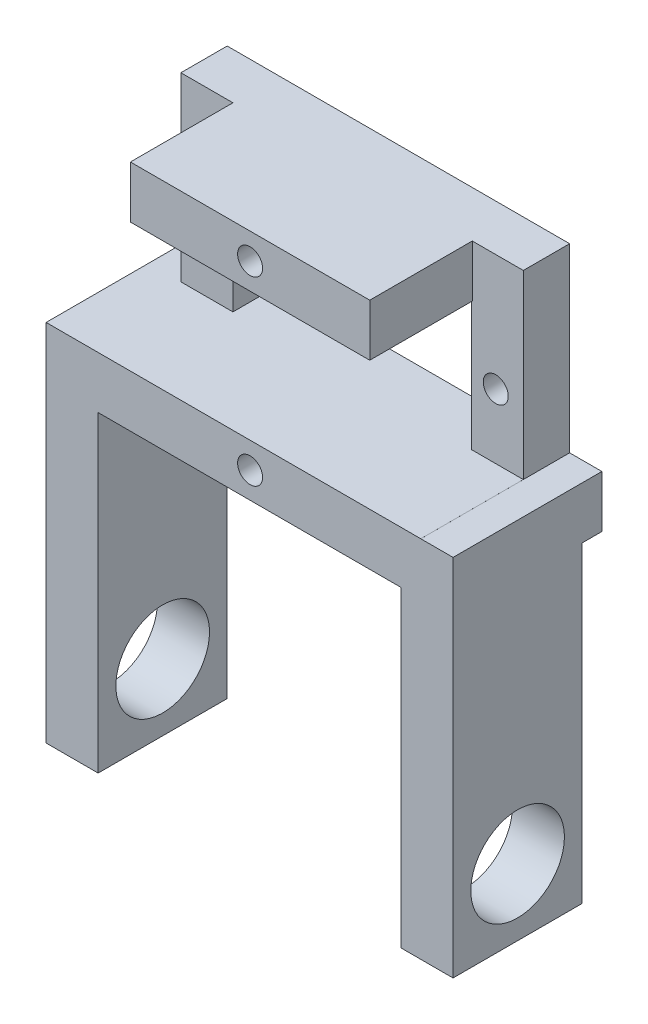
SolidWorks part; units mm, degrees
ref_plane "Front Plane" through (0, 0, 0) normal (0, 0, 1) x (1, 0, 0)
ref_plane "Top Plane" through (0, 0, 0) normal (0, 1, 0) x (1, 0, 0)
ref_plane "Right Plane" through (0, 0, 0) normal (1, 0, 0) x (0, 0, -1)
sketch "Sketch1" plane through (0, 0, 0) normal (0, 0, 1) x (1, 0, 0)
  line L1 (-16.45, 11.2) -> (16.45, 11.2)
  line L2 (-16.45, 11.2) -> (-16.45, -11.2)
  line L3 (-16.45, -11.2) -> (16.45, -11.2)
  line L4 (16.45, 11.2) -> (16.45, -11.2)
  line L5 (-16.45, 11.2) -> (16.45, -11.2) construction
  line L6 (-16.45, -11.2) -> (16.45, 11.2) construction
  point P0 (0, 0)
  dimension "D1" = 32.9
  dimension "22.4" = 22.4
extrude "Boss-Extrude1" add sketch "Sketch1" along normal blind 5
sketch "Sketch2" plane through (0, 0, 5) normal (0, 0, 1) x (1, 0, 0)
  line L0 (0, 0) -> (13.8, 0) construction
  line L1 (-11.45, 6.2) -> (11.45, 6.2)
  line L2 (-11.45, 6.2) -> (-11.45, -6.2)
  line L3 (-11.45, -6.2) -> (11.45, -6.2)
  line L4 (11.45, 6.2) -> (11.45, -6.2)
  line L5 (-11.45, 6.2) -> (11.45, -6.2) construction
  line L6 (-11.45, -6.2) -> (11.45, 6.2) construction
  line L7 (0, 0) -> (-13.8, 0) construction
  circle A0 centre (13.8, 0) radius 1.2
  circle A1 centre (-13.8, 0) radius 1.2
  point P0 (0, 0)
  dimension "D3" = 13.8
  dimension "D1" = 22.9
  dimension "D2" = 13.8
  dimension "12.4" = 12.4
extrude "Cut-Extrude2" cut sketch "Sketch2" against normal blind 5
sketch "Sketch3" plane through (0, 0, 5) normal (0, 0, 1) x (1, 0, 0)
  line L0 (16.45, 11.2) -> (-16.45, 11.2) construction
  line L1 (-11.45, 6.2) -> (11.5469, 6.2)
  line L2 (-11.45, 6.2) -> (-11.45, 11.2)
  line L3 (-11.45, 11.2) -> (11.5469, 11.2)
  line L4 (11.5469, 6.2) -> (11.5469, 11.2)
  line L5 (-16.45, -11.2) -> (16.45, -11.2) construction
  line L6 (-11.45, -6.2) -> (11.5469, -6.2)
  line L7 (-11.45, -6.2) -> (-11.45, -11.2)
  line L8 (-11.45, -11.2) -> (11.5469, -11.2)
  line L9 (11.5469, -6.2) -> (11.5469, -11.2)
extrude "Boss-Extrude2" add sketch "Sketch3" along normal blind 12.3
sketch "Sketch4" plane through (0, 0, 17.3) normal (0, 0, 1) x (1, 0, 0)
  line L0 (0.0484, 11.2) -> (0.0484, 6.2) construction
  line L1 (11.5469, 11.2) -> (-11.45, 11.2) construction
  line L2 (-11.45, 6.2) -> (11.5469, 6.2) construction
  line L3 (0.0484, -6.2) -> (0.0484, -11.2) construction
  line L4 (11.5469, -6.2) -> (-11.45, -6.2) construction
  line L5 (-11.45, -11.2) -> (11.5469, -11.2) construction
  circle A0 centre (0.0484, 8.7) radius 1.2
  circle A1 centre (0.0484, -8.7) radius 1.2
extrude "Cut-Extrude3" cut sketch "Sketch4" against normal blind 5
sketch "Sketch6" plane through (0, 0, 5) normal (0, 0, 1) x (1, 0, 0)
  line L0 (-11.45, 6.2) -> (-11.45, -6.2) construction
  line L1 (-16.45, -11.2) -> (-11.45, -11.2)
  line L2 (-16.45, -11.2) -> (-16.45, -6.2)
  line L3 (-16.45, -6.2) -> (-11.45, -6.2)
  line L4 (-11.45, -11.2) -> (-11.45, -6.2)
  line L5 (-11.45, -6.2) -> (-11.45, -11.2) construction
  line L6 (16.45, -11.2) -> (16.45, 11.2) construction
  line L7 (11.5469, -11.2) -> (16.45, -11.2)
  line L8 (11.5469, -11.2) -> (11.5469, -6.2)
  line L9 (11.5469, -6.2) -> (16.45, -6.2)
  line L10 (16.45, -11.2) -> (16.45, -6.2)
extrude "Boss-Extrude3" add sketch "Sketch6" along normal blind 12.3
sketch "Sketch8" plane through (16.45, 0, 0) normal (1, 0, 0) x (0, 0, -1)
  line L0 (0, -11.2) -> (0, 11.2) construction
  line L1 (-17.3, -11.2) -> (0, -11.2)
  line L2 (-17.3, -11.2) -> (-17.3, -6.2018)
  line L3 (-17.3, -6.2018) -> (0, -6.2018)
  line L4 (0, -11.2) -> (0, -6.2018)
extrude "Boss-Extrude4" add sketch "Sketch8" along normal blind 3.1
sketch "Sketch9" plane through (-16.45, 0, 0) normal (-1, 0, 0) x (0, 0, 1)
  line L1 (0, -11.2) -> (17.3, -11.2)
  line L2 (0, -11.2) -> (0, -6.2)
  line L3 (0, -6.2) -> (17.3, -6.2)
  line L4 (17.3, -11.2) -> (17.3, -6.2)
extrude "Boss-Extrude5" add sketch "Sketch9" along normal blind 3.1
sketch "Sketch10" plane through (0, -11.2, 0) normal (0, -1, 0) x (1, 0, 0)
  line L0 (19.55, 8.65) -> (17.05, 8.65) construction
  line L1 (19.55, 17.3) -> (19.55, 0) construction
  line L2 (-19.55, 8.65) -> (-17.05, 8.65) construction
  line L3 (-19.55, 0) -> (-19.55, 17.3) construction
  line L5 (14.55, 14.85) -> (19.55, 14.85)
  line L6 (14.55, 14.85) -> (14.55, 2.45)
  line L7 (14.55, 2.45) -> (19.55, 2.45)
  line L8 (19.55, 14.85) -> (19.55, 2.45)
  line L9 (14.55, 14.85) -> (19.55, 2.45) construction
  line L10 (14.55, 2.45) -> (19.55, 14.85) construction
  line L11 (-14.55, 14.85) -> (-19.55, 14.85)
  line L12 (-14.55, 14.85) -> (-14.55, 2.45)
  line L13 (-14.55, 2.45) -> (-19.55, 2.45)
  line L14 (-19.55, 14.85) -> (-19.55, 2.45)
  line L15 (-14.55, 14.85) -> (-19.55, 2.45) construction
  line L16 (-14.55, 2.45) -> (-19.55, 14.85) construction
  dimension "D1" = 12.4
sketch "Sketch18" plane through (0, -11.2, 0) normal (0, -1, 0) x (1, 0, 0)
  line L0 (-19.55, 8.65) -> (-17.05, 8.65) construction
  line L1 (-19.55, 0) -> (-19.55, 17.3) construction
  line L2 (19.55, 8.65) -> (17.05, 8.65) construction
  line L4 (19.55, 17.3) -> (19.55, 0) construction
  line L5 (-14.55, 2.45) -> (-19.55, 2.45)
  line L6 (-14.55, 2.45) -> (-14.55, 14.85)
  line L7 (-14.55, 14.85) -> (-19.55, 14.85)
  line L8 (-19.55, 2.45) -> (-19.55, 14.85)
  line L9 (-14.55, 2.45) -> (-19.55, 14.85) construction
  line L10 (-14.55, 14.85) -> (-19.55, 2.45) construction
  line L12 (14.55, 2.45) -> (19.55, 2.45)
  line L13 (14.55, 2.45) -> (14.55, 14.85)
  line L14 (14.55, 14.85) -> (19.55, 14.85)
  line L15 (19.55, 2.45) -> (19.55, 14.85)
  line L16 (14.55, 2.45) -> (19.55, 14.85) construction
  line L17 (14.55, 14.85) -> (19.55, 2.45) construction
  dimension "D1" = 12.4
extrude "Boss-Extrude7" add sketch "Sketch18" along normal blind 30
sketch "Sketch19" plane through (-19.55, 0, 0) normal (-1, 0, 0) x (0, 0, 1)
  line L0 (8.65, -41.2) -> (8.65, -34.8) construction
  line L1 (14.85, -41.2) -> (2.45, -41.2) construction
  circle A0 centre (8.65, -34.8) radius 4.5
extrude "Cut-Extrude6" cut sketch "Sketch19" against normal blind 30
sketch "Sketch20" plane through (19.55, 0, 0) normal (1, 0, 0) x (0, 0, -1)
  line L0 (-8.65, -41.2) -> (-8.65, -34.8) construction
  line L1 (-2.45, -41.2) -> (-14.85, -41.2) construction
  circle A0 centre (-8.65, -34.8) radius 4.5
extrude "Cut-Extrude7" cut sketch "Sketch20" against normal blind 30
extrude "Boss-Extrude6" add sketch "Sketch10" along normal blind 30
sketch "Sketch12" plane through (-19.55, 0, 0) normal (-1, 0, 0) x (0, 0, 1)
sketch "Sketch21" plane through (19.55, 0, 0) normal (1, 0, 0) x (0, 0, -1)
  line L0 (-8.65, -41.2) -> (-8.65, -34.8) construction
  line L1 (-2.45, -41.2) -> (-14.85, -41.2) construction
  circle A0 centre (-8.65, -34.8) radius 4.5
extrude "Cut-Extrude8" cut sketch "Sketch21" against normal blind 10
sketch "Sketch22" plane through (-14.55, 0, 0) normal (1, 0, 0) x (0, 0, -1)
  line L0 (-8.65, -41.2) -> (-8.65, -34.8) construction
  line L1 (-2.45, -41.2) -> (-14.85, -41.2) construction
  circle A0 centre (-8.65, -34.8) radius 4.5
extrude "Cut-Extrude9" cut sketch "Sketch22" against normal blind 10
sketch "Sketch23" plane through (-19.55, 0, 0) normal (-1, 0, 0) x (0, 0, 1)
  line L0 (8.65, -39.3) -> (8.65, -22.3) construction
  line L1 (5.65, -22.3) -> (4.6742, -32.6921)
  line L3 (12.6258, -32.6921) -> (11.65, -22.3)
  circle A0 centre (8.65, -34.8) radius 4.5 construction
  arc A1 (11.65, -22.3) -> (5.65, -22.3) centre (8.65, -22.3) ccw
  arc A2 (4.6742, -32.6921) -> (12.6258, -32.6921) centre (8.65, -34.8) cw
  dimension "D1" = 17
extrude "Cut-Extrude10" cut sketch "Sketch23" against normal blind 3
sketch "Sketch25" plane through (-19.55, 0, 0) normal (-1, 0, 0) x (0, 0, 1)
  line L0 (17.3, 11.2) -> (5, 11.2) construction
  line L1 (17.3, -11.2) -> (14.85, -11.2)
  line L2 (17.3, -11.2) -> (17.3, 11.2)
  line L3 (17.3, 11.2) -> (14.85, 11.2)
  line L4 (14.85, -11.2) -> (14.85, 11.2)
  line L5 (5, 11.2) -> (0, 11.2) construction
  line L6 (0, -11.2) -> (0.55, -11.2)
  line L7 (0, -11.2) -> (0, 11.2)
  line L8 (0, 11.2) -> (0.55, 11.2)
  line L9 (0.55, -11.2) -> (0.55, 11.2)
  dimension "D1" = 0.55
extrude "Cut-Extrude11" cut sketch "Sketch25" against normal through all
